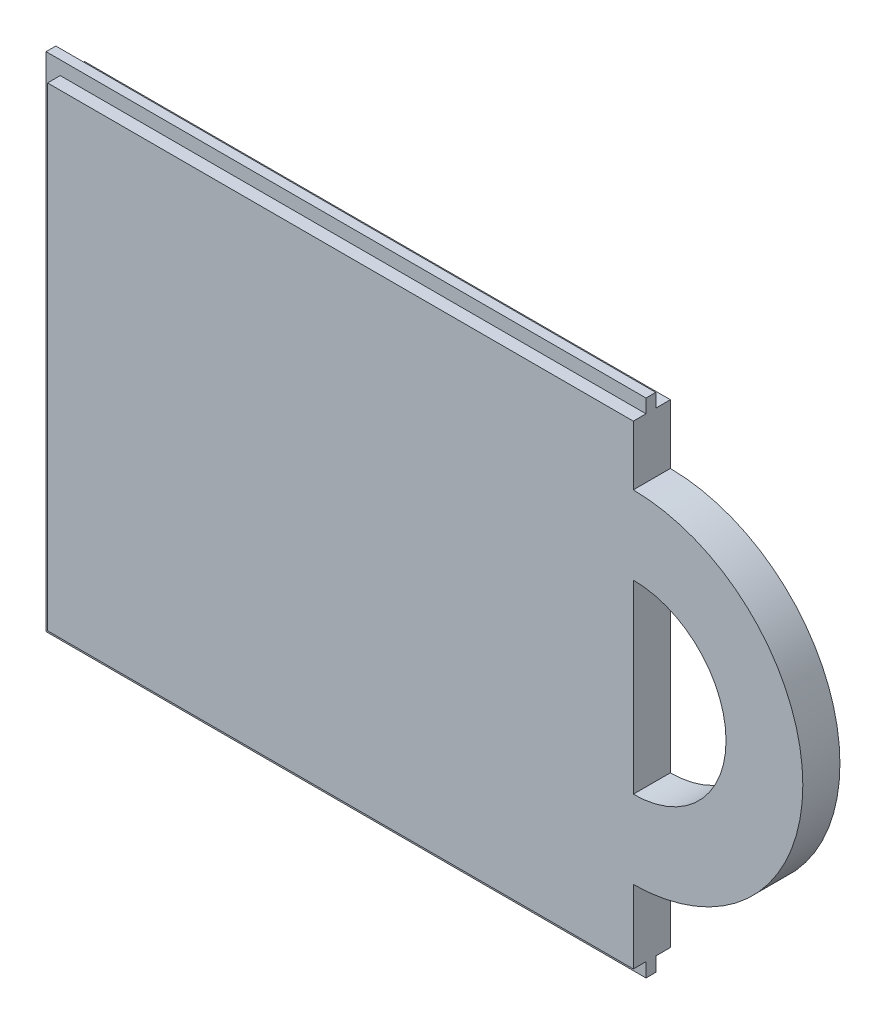
SolidWorks part; units mm, degrees
ref_plane "Front Plane" through (0, 0, 0) normal (0, 0, 1) x (1, 0, 0)
ref_plane "Top Plane" through (0, 0, 0) normal (0, 1, 0) x (1, 0, 0)
ref_plane "Right Plane" through (0, 0, 0) normal (1, 0, 0) x (0, 0, -1)
sketch "Sketch1" plane through (0, 0, 0) normal (0, 0, 1) x (1, 0, 0)
  line L0 (29.1358, 24) -> (-30.8642, 24) construction
  line L1 (29.1358, 23.6) -> (-30.8642, 23.6)
  line L2 (29.1358, 23.6) -> (29.1358, -25)
  line L3 (29.1358, -25) -> (-30.8642, -25)
  line L4 (-30.8642, 23.6) -> (-30.8642, -25)
  line L5 (29.1358, 23.6) -> (-30.8642, -25) construction
  line L6 (29.1358, -25) -> (-30.8642, 23.6) construction
  line L7 (-30.8642, -25) -> (27.1358, -25) construction
  point P0 (0, 0)
  dimension "D1" = 60
  dimension "D2" = 0.4
  dimension "D3" = 0
extrude "Boss-Extrude1" add sketch "Sketch1" along normal blind 3.8
sketch "Sketch2" plane through (0, 0, 3.8) normal (0, 0, 1) x (1, 0, 0)
  line L0 (29.1358, -25) -> (29.1358, 23.6) construction
  line L1 (29.1358, 25) -> (-32.3142, 25)
  line L2 (29.1358, 25) -> (29.1358, -26.45)
  line L3 (29.1358, -26.45) -> (-32.3142, -26.45)
  line L4 (-32.3142, 25) -> (-32.3142, -26.45)
  line L5 (29.1358, 25) -> (-32.3142, -26.45) construction
  line L6 (29.1358, -26.45) -> (-32.3142, 25) construction
  line L7 (29.1358, 23.6) -> (-30.8642, 23.6) construction
  line L8 (-32.3642, -26.5) -> (29.1358, -26.5) construction
  line L9 (-32.3642, 25.5) -> (-32.3642, -26.5) construction
  point P0 (0, 0)
  dimension "D1" = 0
  dimension "D2" = 1.4
  dimension "D3" = 0.05
  dimension "D4" = 0.05
sketch "Sketch3" plane through (0, 0, 3.8) normal (0, 0, 1) x (1, 0, 0)
  line L1 (-30.8642, -25) -> (29.1358, -25) construction
  circle A0 centre (29.0017, 0) radius 17.5
  dimension "D1" = 35
  dimension "D2" = 25
extrude "Boss-Extrude3" add sketch "Sketch3" against normal up to surface (3.8 mm away) up to face at (-0.8642, -0.7, 0)
sketch "Sketch4" plane through (0, 0, 3.8) normal (0, 0, 1) x (1, 0, 0)
  line L0 (29.1358, 25) -> (29.1358, -26.45) construction
  line L1 (29.1358, 9.4995) -> (29.1358, -9.4995)
  arc A0 (29.1358, 9.4995) -> (29.1358, -9.4995) centre (29.1358, 0) cw
  dimension "D1" = 0
  dimension "4mm" = 8
extrude "Cut-Extrude2" cut sketch "Sketch4" against normal up to next
extrude "Boss-Extrude4" add sketch "Sketch2" against normal blind 1 from offset 1.3
